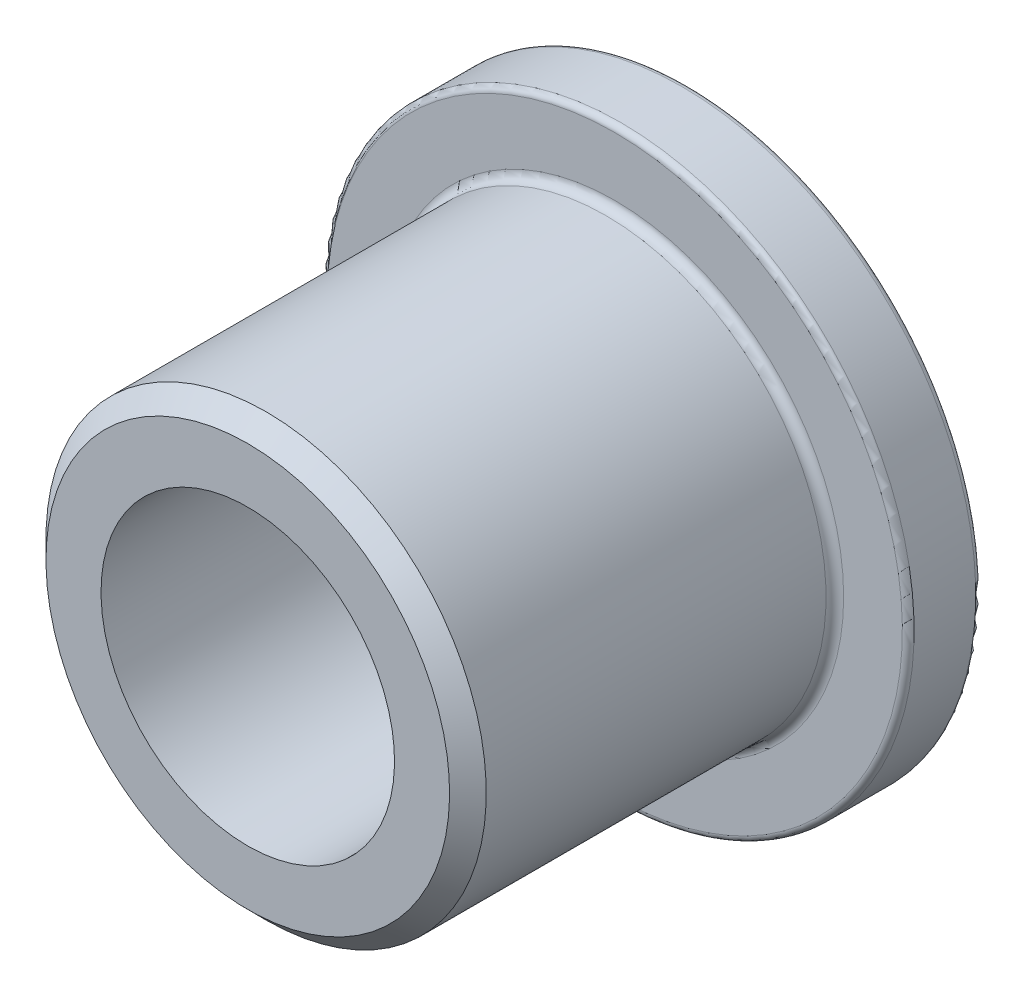
SolidWorks part; units mm, degrees
ref_plane "Front Plane" through (0, 0, 0) normal (0, 0, 1) x (1, 0, 0)
ref_plane "Top Plane" through (0, 0, 0) normal (0, 1, 0) x (1, 0, 0)
ref_plane "Right Plane" through (0, 0, 0) normal (1, 0, 0) x (0, 0, -1)
sketch "Sketch1" plane through (0, 0, 0) normal (1, 0, 0) x (0, 0, -1)
  line L0 (-4.7625, 0) -> (4.7625, 0) construction
  line L1 (4.7625, 6.35) -> (4.7625, -6.35) construction
  line L2 (-4.7625, 4.7625) -> (-4.7625, -4.7625) construction
  line L3 (4.7625, 6.35) -> (3.175, 6.35) construction
  line L4 (4.7625, -6.35) -> (3.175, -6.35) construction
  point P2 (0, 0)
  point P7 (-4.7625, 0)
  point P8 (-4.7625, -3.175)
  point P9 (4.7625, 0)
  point P11 (-4.7625, 3.175)
  dimension "Flange OD" = 12.7
  dimension "OD" = 9.525
  dimension "ID" = 6.35
  dimension "Length" = 9.525
  dimension "Flange Thickness" = 1.5875
sketch "Sketch2" plane through (0, 0, 0) normal (0, 0, 1) x (1, 0, 0)
  line L0 (-6.35, 0) -> (6.35, 0) construction
  line L1 (0, -6.35) -> (0, 6.35) construction
  circle A0 centre (0, 0) radius 3.175 construction
  circle A1 centre (0, 0) radius 4.7625 construction
  circle A2 centre (0, 0) radius 6.35 construction
  dimension "ID" = 6.35
  dimension "OD" = 9.525
  dimension "Flange OD" = 12.7
sketch "Sketch3" plane through (0, 0, 0) normal (1, 0, 0) x (0, 0, -1)
  line L0 (-4.7625, 3.175) -> (4.7625, 3.175)
  line L1 (4.7625, 6.35) -> (4.7625, -6.35) construction
  line L2 (4.7625, 3.175) -> (4.7625, 6.35)
  line L3 (4.7625, 6.35) -> (3.175, 6.35)
  line L4 (3.175, 6.35) -> (3.175, 4.7625)
  line L5 (3.175, 4.7625) -> (-4.7625, 4.7625)
  line L6 (-4.7625, 4.7625) -> (-4.7625, 3.175)
  line L7 (-4.7625, 0) -> (4.7625, 0) construction
revolve "Revolve1" add sketch "Sketch3" angle 360 about L7
chamfer "Chamfer1" distance 0.3969 angle 45 1 edges at (0, -4.7625, 4.7625)
fillet "Fillet1" radius 0.1905 1 edges at (0, -4.7625, -3.175)
fillet "Fillet2" radius 0.127 2 edges at (0, -6.35, -4.7625) (0, -6.35, -3.175)
chamfer "Chamfer2" distance 0.3175 angle 45 1 edges at (0, -3.175, -4.7625)
equation "\"D1@Chamfer1\"=((\"OD@Sketch1\"-\"ID@Sketch1\")/2)*.25"
equation "\"D1@Fillet1\"=\"OD@Sketch1\"*.02"
equation "\"D1@Fillet2\"=\"Flange OD@Sketch1\"*.01"
equation "\"D1@Chamfer2\"=\"ID@Sketch1\"*.05"
